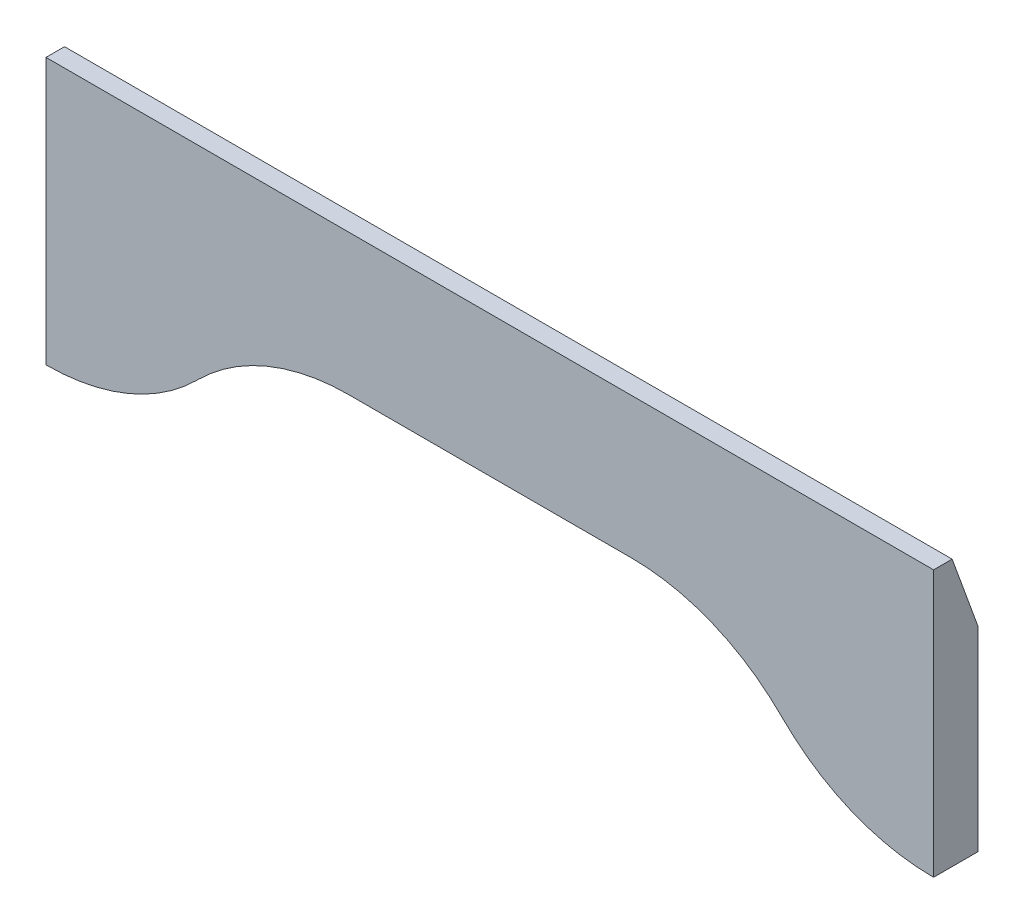
SolidWorks part; units mm, degrees
ref_plane "Front Plane" through (0, 0, 0) normal (0, 0, 1) x (1, 0, 0)
ref_plane "Top Plane" through (0, 0, 0) normal (0, 1, 0) x (1, 0, 0)
ref_plane "Right Plane" through (0, 0, 0) normal (1, 0, 0) x (0, 0, -1)
sketch "Sketch1" plane through (0, 0, 0) normal (0, 0, 1) x (1, 0, 0)
  line L1 (0, 0) -> (127, 0)
  line L2 (0, 0) -> (0, 38.1)
  line L3 (0, 38.1) -> (127, 38.1)
  line L4 (127, 0) -> (127, 38.1)
  dimension "D1" = 127
  dimension "D2" = 38.1
extrude "Boss-Extrude1" add sketch "Sketch1" along normal blind 6.35
sketch "Sketch2" plane through (0, 0, 6.35) normal (0, 0, 1) x (1, 0, 0)
  line L0 (12.7, 0) -> (30.6605, 17.9605)
  line L1 (0, 0) -> (127, 0) construction
  line L2 (30.6605, 17.9605) -> (96.3395, 17.9605)
  line L3 (96.3395, 17.9605) -> (114.3, 0)
  line L5 (12.7, 0) -> (114.3, 0)
  dimension "D1" = 12.7
  dimension "D2" = 12.7
  dimension "D3" = 45
  dimension "D4" = 25.4
  dimension "D5" = 45
extrude "Cut-Extrude1" cut sketch "Sketch2" against normal blind 6.35
fillet "Fillet1" radius 30.48 4 edges at (114.3, 0, 3.175) (96.3395, 17.9605, 3.175) (30.6605, 17.9605, 3.175) (12.7, 0, 3.175)
chamfer "Chamfer1" distance 10.16 angle 20 1 edges at (63.5, 38.1, 0)
